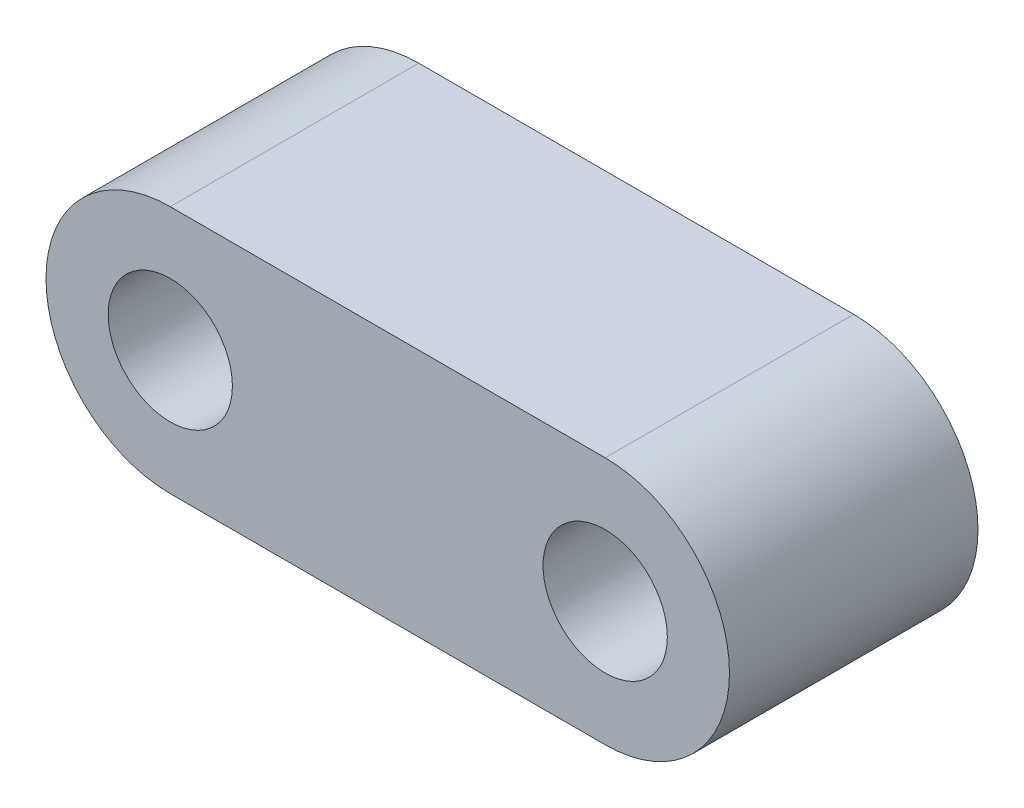
SolidWorks part; units mm, degrees
ref_plane "Alzado" through (0, 0, 0) normal (0, 0, 1) x (1, 0, 0)
ref_plane "Planta" through (0, 0, 0) normal (0, 1, 0) x (1, 0, 0)
ref_plane "Vista lateral" through (0, 0, 0) normal (1, 0, 0) x (0, 0, -1)
sketch "Croquis1" plane through (0, 0, 0) normal (0, 0, 1) x (1, 0, 0)
  line L0 (0, 0) -> (70, 0) construction
  line L1 (70, -20) -> (0, -20)
  line L2 (0, 20) -> (70, 20)
  circle A0 centre (0, 0) radius 10
  circle A1 centre (0, 0) radius 20
  circle A2 centre (70, 0) radius 10
  circle A3 centre (70, 0) radius 20
  dimension "D1" = 20
  dimension "D3" = 20
  dimension "D4" = 40
  dimension "D5" = 40
  dimension "D2" = 70
extrude "Saliente-Extruir1" add sketch "Croquis1" along normal mid plane 40
